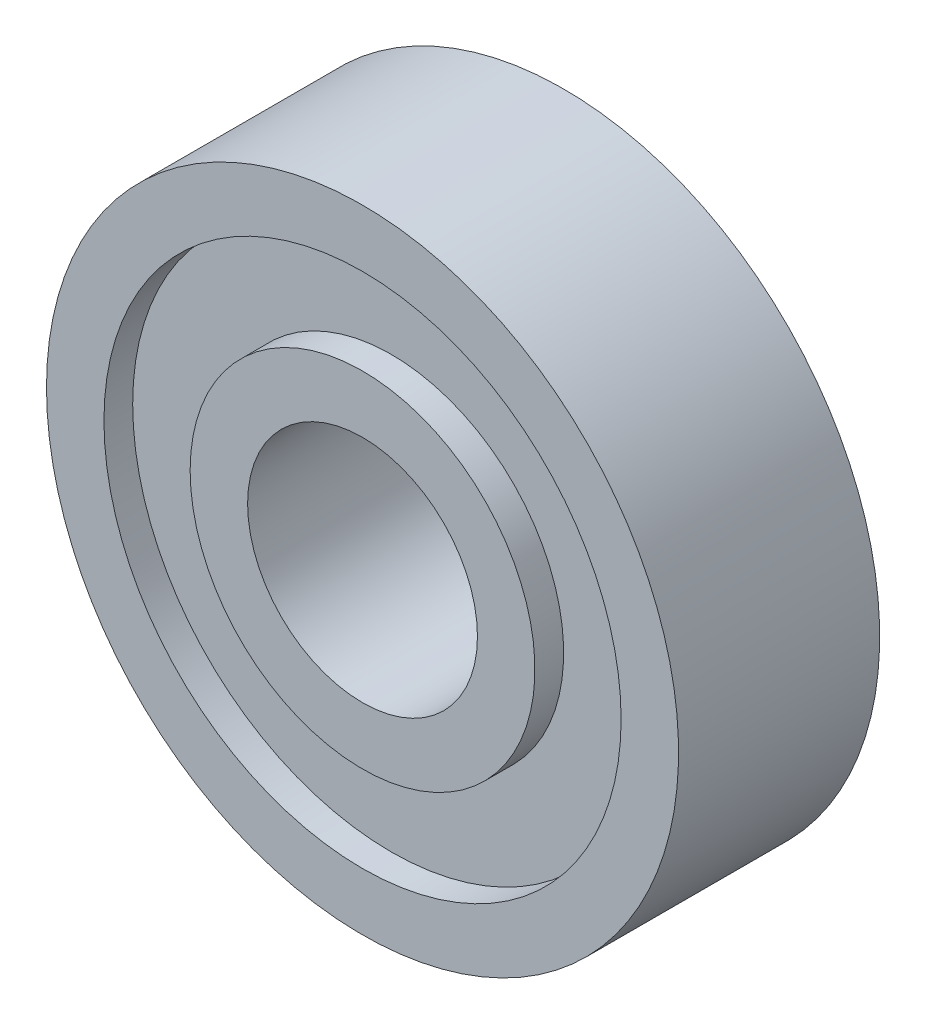
SolidWorks part; units mm, degrees
ref_plane "Front Plane" through (0, 0, 0) normal (0, 0, 1) x (1, 0, 0)
ref_plane "Top Plane" through (0, 0, 0) normal (0, 1, 0) x (1, 0, 0)
ref_plane "Right Plane" through (0, 0, 0) normal (1, 0, 0) x (0, 0, -1)
ref_plane "Plane1" through (0, 0, 0) normal (0, -1, 0) x (1, 0, 0)
sketch "Sketch1" plane through (0, 0, 0) normal (0, -1, 0) x (1, 0, 0)
  line L0 (6, -3.5) -> (6, -2.5)
  line L1 (6, -2.5) -> (9, -2.5)
  line L2 (9, -2.5) -> (9, -3.5)
  line L3 (9, -3.5) -> (11, -3.5)
  line L4 (11, -3.5) -> (11, 3.5)
  line L5 (11, 3.5) -> (9, 3.5)
  line L6 (9, 3.5) -> (9, 2.5)
  line L7 (9, 2.5) -> (6, 2.5)
  line L8 (6, 2.5) -> (6, 3.5)
  line L9 (6, 3.5) -> (4, 3.5)
  line L10 (4, 3.5) -> (4, -3.5)
  line L11 (4, -3.5) -> (6, -3.5)
  line L12 (0, 3.5) -> (0, -3.5) construction
revolve "Revolve1" add sketch "Sketch1" angle 360 about L12
